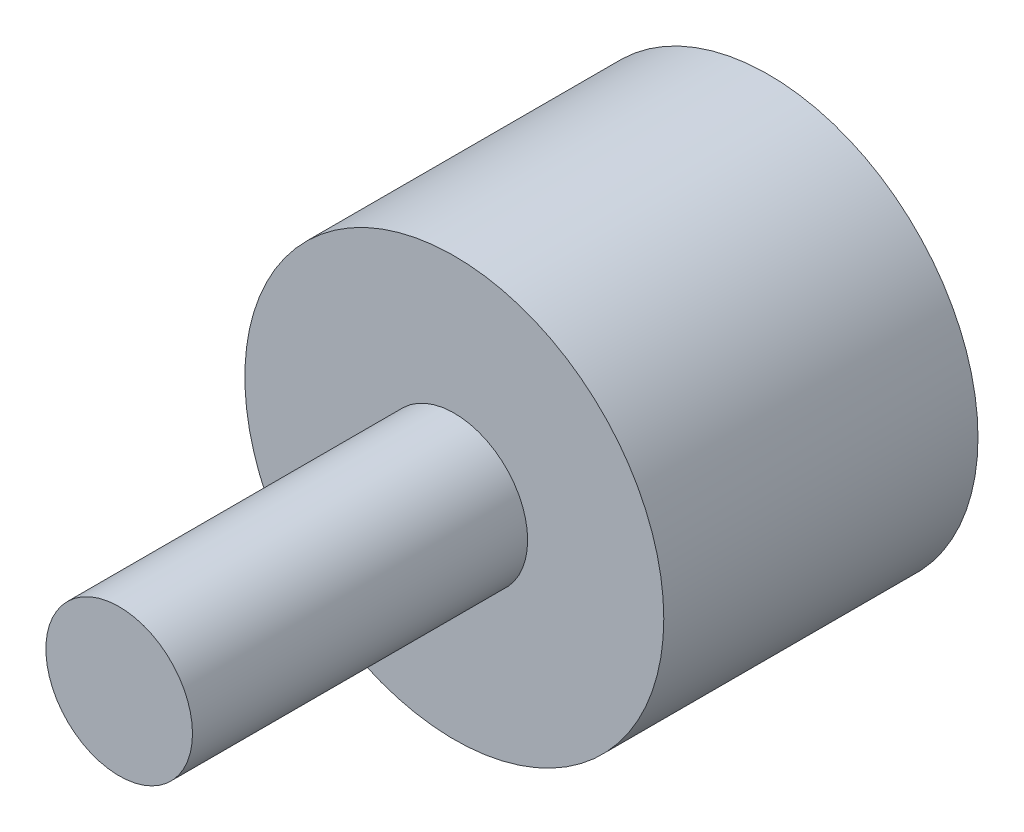
SolidWorks part; units mm, degrees
ref_plane "Plan de face" through (0, 0, 0) normal (0, 0, 1) x (1, 0, 0)
ref_plane "Plan de dessus" through (0, 0, 0) normal (0, 1, 0) x (1, 0, 0)
ref_plane "Plan de droite" through (0, 0, 0) normal (1, 0, 0) x (0, 0, -1)
sketch "Esquisse1" plane through (0, 0, 0) normal (0, 0, 1) x (1, 0, 0)
  circle A0 centre (0, 0) radius 10
  dimension "D1" = 20
extrude "Boss.-Extru.1" add sketch "Esquisse1" along normal blind 15
sketch "Esquisse2" plane through (0, 0, 15) normal (0, 0, 1) x (1, 0, 0)
  circle A0 centre (0, 0) radius 3.5
  dimension "D1" = 7
extrude "Boss.-Extru.2" add sketch "Esquisse2" along normal blind 16
sketch "Esquisse3" plane through (0, 0, 0) normal (0, 1, 0) x (1, 0, 0)
  line L0 (0, -34.7899) -> (0, 23.842) construction
  line L1 (0, 3) -> (0, -9)
  arc A0 (0, 3) -> (0, -9) centre (0, -3) cw
  dimension "D1" = 6
  dimension "D2" = 3
revolve "Révolution1" add sketch "Esquisse3" angle 360 about L0
